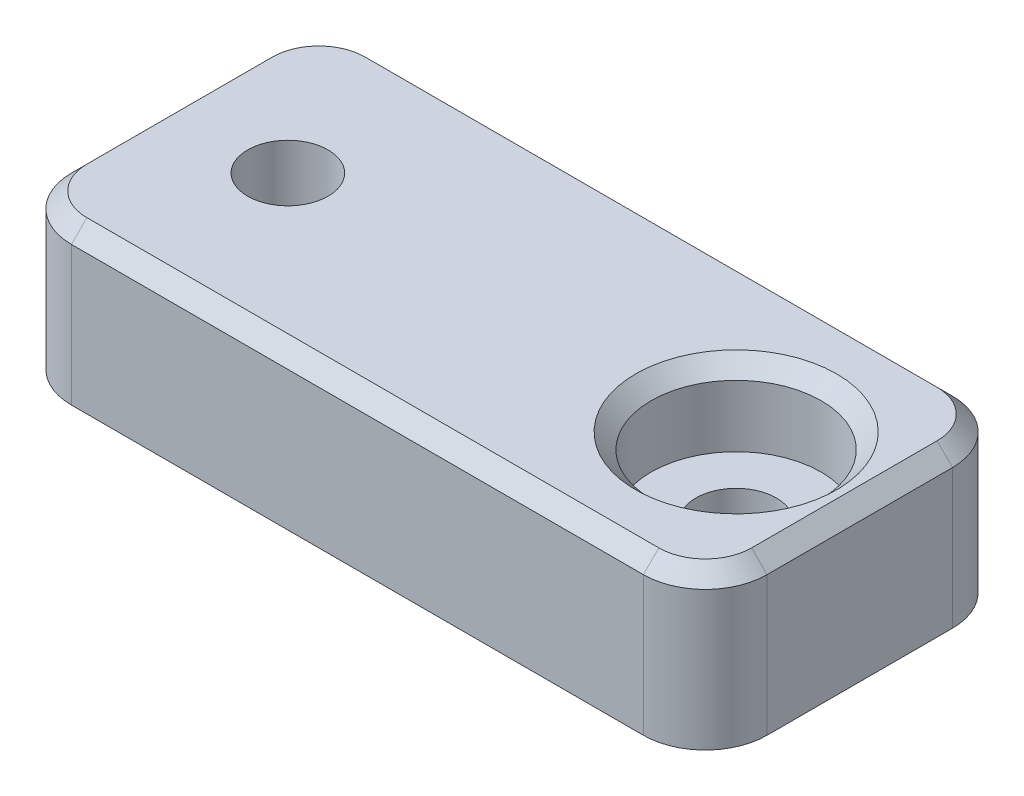
SolidWorks part; units mm, degrees
material "ABS"
ref_plane "Front Plane" through (0, 0, 0) normal (0, 0, 1) x (1, 0, 0)
ref_plane "Top Plane" through (0, 0, 0) normal (0, 1, 0) x (1, 0, 0)
ref_plane "Right Plane" through (0, 0, 0) normal (1, 0, 0) x (0, 0, -1)
sketch "Sketch1" plane through (0, 0, 0) normal (1, 0, 0) x (0, 0, -1)
  line L0 (-10, 5) -> (10, 5)
  line L1 (-10, 5) -> (-10, -5)
  line L2 (10, 5) -> (10, -5)
  line L3 (-10, -5) -> (-2.95, -5)
  line L4 (-10, 5) -> (10, -5) construction
  line L5 (10, 5) -> (-10, -5) construction
  line L6 (2.95, -5) -> (2.8188, -6.5)
  line L7 (2.8188, -6.5) -> (-2.8188, -6.5)
  line L8 (-2.8188, -6.5) -> (-2.95, -5)
  line L9 (2.95, -5) -> (10, -5)
  point P1 (0, 0)
  point P3 (0, -6.5)
  dimension "D1" = 10
  dimension "D2" = 20
  dimension "D3" = 5.9
  dimension "D4" = 1.5
  dimension "D5" = 95
  dimension "D6" = 95
extrude "Boss-Extrude1" add sketch "Sketch1" along normal mid plane 45
sketch "Sketch2" plane through (0, 5, 0) normal (0, 1, 0) x (1, 0, 0)
  line L0 (0, 10) -> (0, -10) construction
  line L1 (22.5, 10) -> (-22.5, 10) construction
  line L2 (22.5, -10) -> (-22.5, -10) construction
  line L3 (-22.5, 10) -> (-22.5, -10) construction
  circle A0 centre (-14.5, 0) radius 2.6
  circle A1 centre (14.5, 0) radius 2.6
  dimension "D2" = 5.2
  dimension "D1" = 8
extrude "Cut-Extrude1" cut sketch "Sketch2" against normal up to surface (11.5 mm away) up to face at (0, -6.5, 0)
sketch "Sketch3" plane through (0, -5, 0) normal (0, -1, 0) x (1, 0, 0)
  line L0 (22.5, 10) -> (-22.5, 10) construction
  line L1 (22.5, -10) -> (8.5, -10)
  line L2 (22.5, -10) -> (22.5, 10)
  line L3 (22.5, 10) -> (8.5, 10)
  line L4 (8.5, -10) -> (8.5, 10)
  line L5 (0, -10) -> (0, 10) construction
  line L6 (22.5, -10) -> (-22.5, -10) construction
  line L7 (-8.5, -10) -> (-8.5, 10)
  line L8 (-22.5, 10) -> (-8.5, 10)
  line L9 (-22.5, -10) -> (-22.5, 10)
  line L10 (-22.5, -10) -> (-8.5, -10)
  dimension "D1" = 14
extrude "Cut-Extrude2" cut sketch "Sketch3" along normal up to surface (1.5 mm away) up to face at (14.5, -6.5, 2.6)
draft "Draft1" type of draft neutral plane draft angle 45 faces to draft 2 face at (8.5, -5.75, 0) face at (-8.5, -5.75, 0) neutral plane through (22.5, -6.5, -2.8188) neutral plane normal (0, -1, 0) parameters "D1"=45
fillet "Fillet1" radius 4 4 edges at (22.5, 0, -10) (22.5, 0, 10) (-22.5, 0, -10) (-22.5, 0, 10)
sketch "Sketch6" plane through (0, 5, 0) normal (0, 1, 0) x (1, 0, 0)
  circle A0 centre (14.5, 0) radius 5.5
  dimension "D1" = 11
extrude "Cut-Extrude3" cut sketch "Sketch6" against normal blind 5
chamfer "Chamfer2" distance 1 angle 45 9 edges at (-21.3284, 5, 8.8284) (0, 5, 10) (-22.5, 5, 0) (21.3284, 5, 8.8284) (-21.3284, 5, -8.8284) (22.5, 5, 0) (0, 5, -10) (21.3284, 5, -8.8284) (14.5, 5, 5.5)
